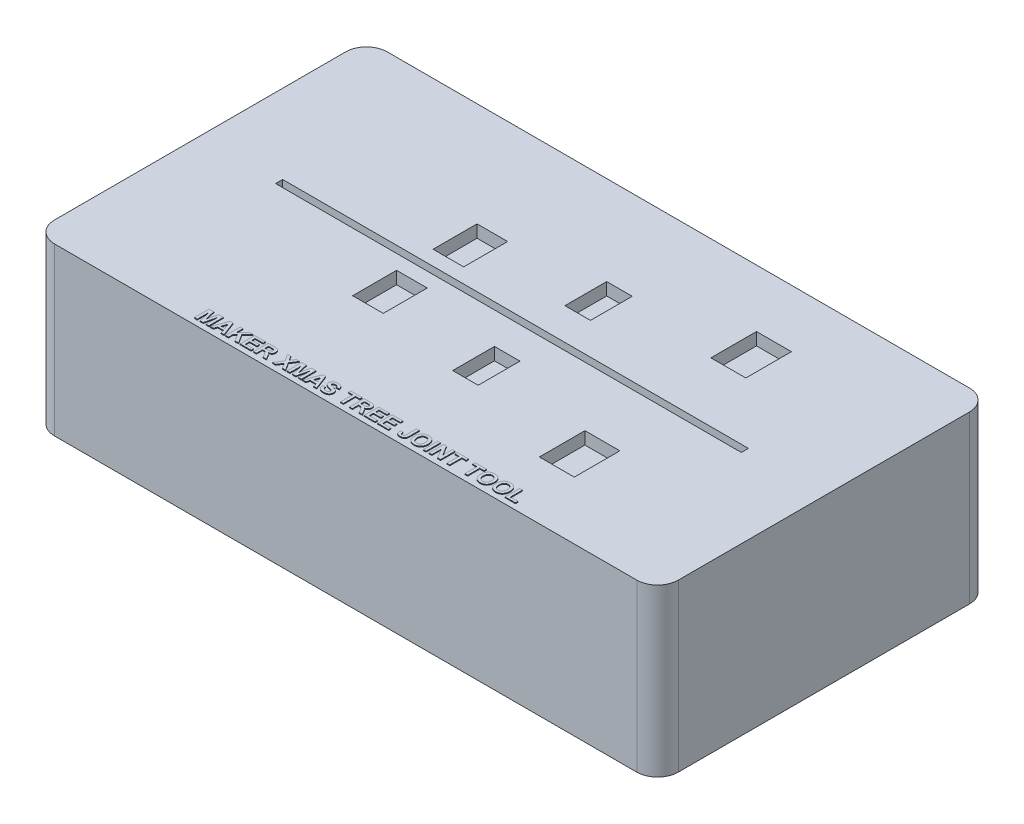
SolidWorks part; units mm, degrees
ref_plane "Alzado" through (0, 0, 0) normal (0, 0, 1) x (1, 0, 0)
ref_plane "Planta" through (0, 0, 0) normal (0, 1, 0) x (1, 0, 0)
ref_plane "Vista lateral" through (0, 0, 0) normal (1, 0, 0) x (0, 0, -1)
sketch "Croquis1" plane through (0, 0, 0) normal (0, 1, 0) x (1, 0, 0)
  line L1 (-70, 40) -> (70, 40)
  line L2 (-75, 35) -> (-75, -35)
  line L3 (-70, -40) -> (70, -40)
  line L4 (75, 35) -> (75, -35)
  line L5 (-75, 40) -> (75, -40) construction
  line L6 (-75, -40) -> (75, 40) construction
  arc A0 (-70, -40) -> (-75, -35) centre (-70, -35) cw
  arc A1 (75, -35) -> (70, -40) centre (70, -35) cw
  arc A2 (75, 35) -> (70, 40) centre (70, 35) ccw
  arc A3 (-70, 40) -> (-75, 35) centre (-70, 35) ccw
  point P0 (0, 0)
  dimension "D3" = 5
  dimension "D1" = 150
  dimension "D2" = 80
extrude "Saliente-Extruir1" add sketch "Croquis1" along normal blind 40
sketch "Croquis2" plane through (0, 40, 0) normal (0, 1, 0) x (1, 0, 0)
  line L1 (-56, 0.85) -> (56, 0.85)
  line L2 (-56, 0.85) -> (-56, -0.85)
  line L3 (-56, -0.85) -> (56, -0.85)
  line L4 (56, 0.85) -> (56, -0.85)
  line L5 (-56, 0.85) -> (56, -0.85) construction
  line L6 (-56, -0.85) -> (56, 0.85) construction
  point P0 (0, 0)
  dimension "D1" = 112
  dimension "D2" = 1.7
extrude "Cortar-Extruir1" cut sketch "Croquis2" against normal blind 37
sketch "Croquis3" plane through (0, 40, 0) normal (0, 1, 0) x (1, 0, 0)
  line L1 (-55, 34) -> (55, 34)
  line L2 (-55, 34) -> (-55, -34)
  line L3 (-55, -34) -> (55, -34)
  line L4 (55, 34) -> (55, -34)
  line L5 (-55, 34) -> (55, -34) construction
  line L6 (-55, -34) -> (55, 34) construction
  point P0 (0, 0)
  dimension "D1" = 110
  dimension "D2" = 68
sketch "Croquis4" plane through (0, 40, 0) normal (0, 1, 0) x (1, 0, 0)
  text T0 "MAKER XMAS TREE JOINT TOOL" font "Arial" height 3.5
extrude "Saliente-Extruir2" add sketch "Croquis4" along normal blind 0.2
sketch "Croquis5" plane through (0, 40, 0) normal (0, -1, 0) x (1, 0, 0)
  line L1 (41.0292, -26.1587) -> (32.6396, -26.1587)
  line L2 (41.0292, -26.1587) -> (41.0292, -15.1943)
  line L3 (41.0292, -15.1943) -> (32.6396, -15.1943)
  line L4 (32.6396, -26.1587) -> (32.6396, -15.1943)
  line L5 (10.3573, -18.5498) -> (4.2231, -18.5498)
  line L6 (10.3573, -18.5498) -> (10.3573, -8.5093)
  line L7 (10.3573, -8.5093) -> (4.2231, -8.5093)
  line L8 (4.2231, -18.5498) -> (4.2231, -8.5093)
  line L9 (-16.028, -14.9799) -> (-23.3823, -14.9799)
  line L10 (-16.028, -14.9799) -> (-16.028, -4.4031)
  line L11 (-16.028, -4.4031) -> (-23.3823, -4.4031)
  line L12 (-23.3823, -14.9799) -> (-23.3823, -4.4031)
  line L13 (-16.0147, 4.374) -> (-23.3784, 4.374)
  line L14 (-16.0147, 4.374) -> (-16.0147, 14.9442)
  line L15 (-16.0147, 14.9442) -> (-23.3784, 14.9442)
  line L16 (-23.3784, 4.374) -> (-23.3784, 14.9442)
  line L17 (10.3649, 8.4501) -> (4.2396, 8.4501)
  line L18 (10.3649, 8.4501) -> (10.3649, 18.496)
  line L19 (10.3649, 18.496) -> (4.2396, 18.496)
  line L20 (4.2396, 8.4501) -> (4.2396, 18.496)
  line L21 (41.0525, 15.1152) -> (32.6531, 15.1152)
  line L22 (41.0525, 15.1152) -> (41.0525, 26.072)
  line L23 (41.0525, 26.072) -> (32.6531, 26.072)
  line L24 (32.6531, 15.1152) -> (32.6531, 26.072)
extrude "Cortar-Extruir2" cut sketch "Croquis5" along normal blind 3
